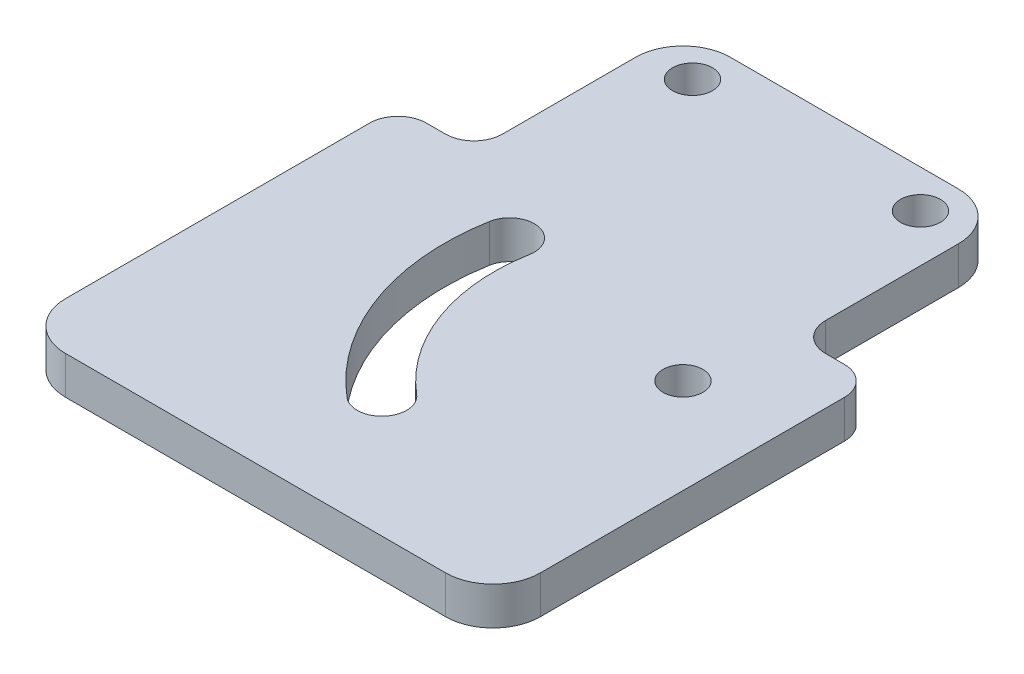
SolidWorks part; units mm, degrees
material "6061 合金"
ref_plane "前视基准面" through (0, 0, 0) normal (0, 0, 1) x (1, 0, 0)
ref_plane "上视基准面" through (0, 0, 0) normal (0, 1, 0) x (1, 0, 0)
ref_plane "右视基准面" through (0, 0, 0) normal (1, 0, 0) x (0, 0, -1)
sketch "草图1" plane through (0, 0, 0) normal (0, 1, 0) x (1, 0, 0)
  line L0 (-1000, 0) -> (49000, 0) construction
  line L1 (0, -1000) -> (0, 49000) construction
  line L2 (0, 0) -> (32139.3805, 38302.2222) construction
  line L3 (0, 0) -> (-49240.3877, 8682.4089) construction
  line L9 (-40, 10) -> (10, 10)
  line L10 (-40, 10) -> (-40, -30)
  line L11 (-40, -30) -> (10, -30)
  line L12 (10, 10) -> (10, -30)
  circle A0 centre (0, 0) radius 2.1
  arc A1 (-22.1582, 3.9071) -> (-14.4627, -17.236) centre (0, 0) ccw construction
  arc A6 (-24.7187, 4.3586) -> (-16.134, -19.2277) centre (0, 0) ccw
  arc A7 (-19.5977, 3.4556) -> (-12.7915, -15.2443) centre (0, 0) ccw
  arc A8 (-19.5977, 3.4556) -> (-24.7187, 4.3586) centre (-22.1582, 3.9071) ccw
  arc A9 (-16.134, -19.2277) -> (-12.7915, -15.2443) centre (-14.4627, -17.236) ccw
  point P5 (-21.1431, -7.6955)
  dimension "D1" = 4.2
  dimension "D2" = 50
  dimension "D3" = 22.5
  dimension "D5" = 2.6
  dimension "D4" = 10
  dimension "D6" = 10
  dimension "D7" = 10
  dimension "D8" = 30
  dimension "D9" = 40
extrude "主板" add sketch "草图1" along normal blind 4
sketch "草图2" plane through (0, 4, 0) normal (0, 1, 0) x (1, 0, 0)
  line L0 (-40, 10) -> (-40, -30) construction
  line L1 (-32, 24) -> (2, 24)
  line L2 (-32, 24) -> (-32, 32)
  line L3 (-32, 32) -> (2, 32)
  line L4 (2, 24) -> (2, 32)
  line L5 (-15, 32) -> (-15, 24) construction
  line L6 (-32, 28) -> (2, 28) construction
  line L7 (10, -30) -> (10, 10) construction
  line L8 (10, 10) -> (-40, 10) construction
  line L13 (-32, 24) -> (2, 24)
  line L14 (-32, 24) -> (-32, 10)
  line L15 (-32, 10) -> (2, 10)
  line L16 (2, 24) -> (2, 10)
  circle A0 centre (-3, 28) radius 2.1
  circle A1 centre (-27, 28) radius 2.1
  point P0 (-15, 28)
  line M9 (10, 10) -> (-40, 10)
  dimension "D3" = 4.2
  dimension "D4" = 24
  dimension "D1" = 8
  dimension "D2" = 34
  dimension "D5" = 14
extrude "固定板" add sketch "草图2" against normal through all contours L16 L1 L14 M9 | L1 L4 L3 L2 A0 A1
fillet "圆角3" radius 3 4 edges at (10, 2, -10) (2, 2, -10) (-40, 2, -10) (-32, 2, -10)
fillet "圆角5" radius 5 4 edges at (2, 2, -32) (-40, 2, 30) (10, 2, 30) (-32, 2, -32)
